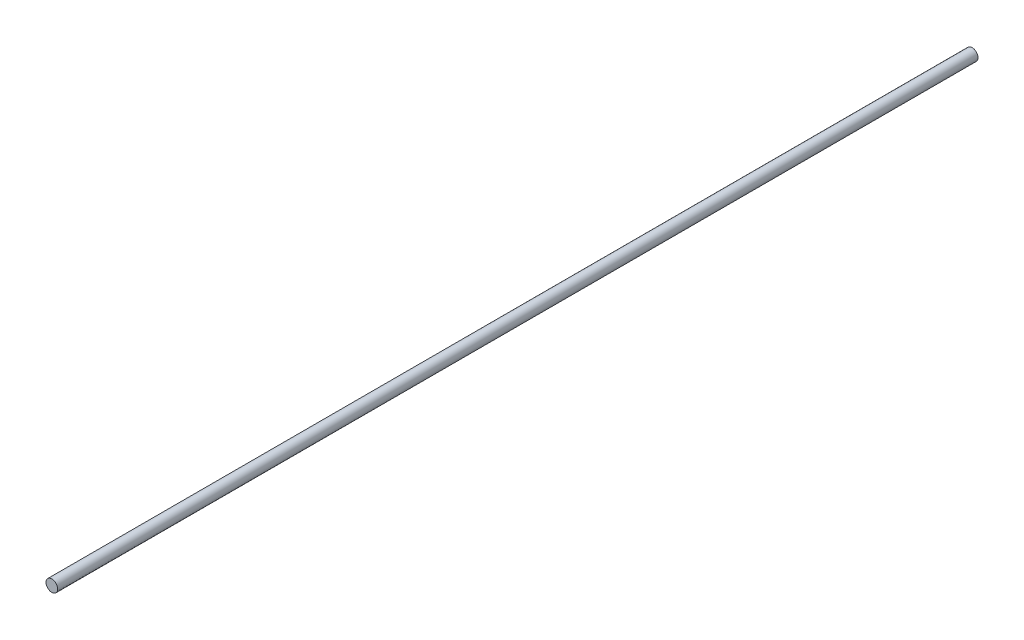
SolidWorks part; units mm, degrees
material "PLA Aero Bambu"
ref_plane "Front Plane" through (0, 0, 0) normal (0, 0, 1) x (1, 0, 0)
ref_plane "Top Plane" through (0, 0, 0) normal (0, 1, 0) x (1, 0, 0)
ref_plane "Right Plane" through (0, 0, 0) normal (1, 0, 0) x (0, 0, -1)
sketch "Sketch1" plane through (0, 0, 0) normal (0, 0, 1) x (1, 0, 0)
  circle A0 centre (0, 0) radius 0.975
  dimension "D1" = 1.95
extrude "Boss-Extrude1" add sketch "Sketch1" along normal blind 153.75
sketch "Sketch2" plane through (0, 0, 0) normal (0, 0, -1) x (-1, 0, 0)
  line L1 (-0.5, 0.5) -> (0.5, 0.5)
  line L2 (-0.5, 0.5) -> (-0.5, -0.5)
  line L3 (-0.5, -0.5) -> (0.5, -0.5)
  line L4 (0.5, 0.5) -> (0.5, -0.5)
  point P4 (0, -0.5)
  point P6 (0.5, 0)
  dimension "D1" = 1
extrude "Cut-Extrude1" cut sketch "Sketch2" against normal blind 5
